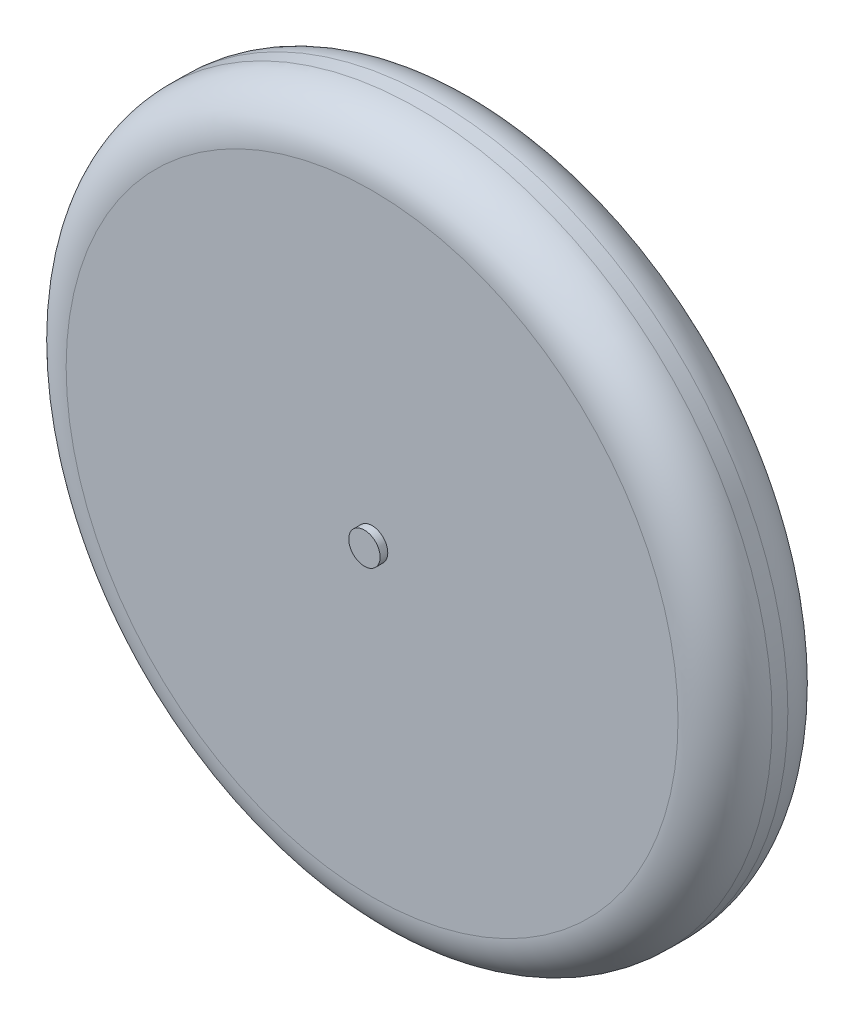
SolidWorks part; units mm, degrees
material "Rubber"
ref_plane "Front Plane" through (0, 0, 0) normal (0, 0, 1) x (1, 0, 0)
ref_plane "Top Plane" through (0, 0, 0) normal (0, 1, 0) x (1, 0, 0)
ref_plane "Right Plane" through (0, 0, 0) normal (1, 0, 0) x (0, 0, -1)
sketch "Sketch1" plane through (0, 0, 0) normal (0, 1, 0) x (1, 0, 0)
  line L0 (0, 0) -> (2.54, 0)
  line L1 (2.54, 0) -> (2.54, -1.2395)
  line L2 (2.54, -1.2395) -> (49.53, -1.2395)
  line L3 (57.15, -8.8595) -> (57.15, -11.3995)
  line L4 (0, -20.2589) -> (0, 40.5107) construction
  line L5 (2.54, -19.0195) -> (49.53, -19.0195)
  line L6 (2.54, -20.2589) -> (2.54, -19.0195)
  line L7 (0, -20.2589) -> (2.54, -20.2589)
  line L8 (0, 0) -> (0, -20.2589)
  arc A0 (49.53, -1.2395) -> (57.15, -8.8595) centre (49.53, -8.8595) cw
  arc A1 (49.53, -19.0195) -> (57.15, -11.3995) centre (49.53, -11.3995) ccw
  point P8 (57.15, -1.2395)
  point P16 (57.15, -19.0195)
  dimension "D4" = 7.62
  dimension "D1" = 2.54
  dimension "D3" = 57.15
revolve "Revolve1" add sketch "Sketch1" angle 360 about L4
